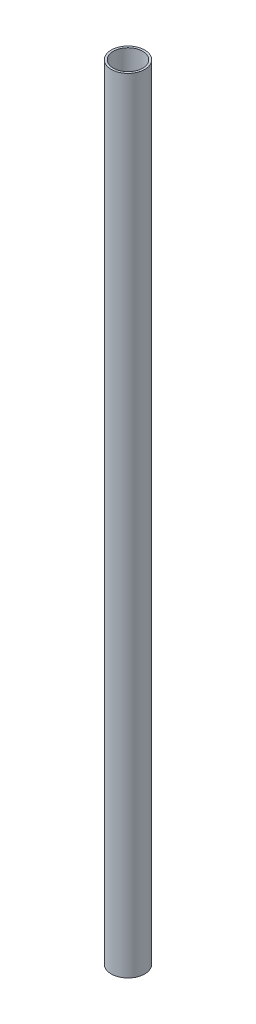
SolidWorks part; units mm, degrees
ref_plane "Спереди" through (0, 0, 0) normal (0, 0, 1) x (1, 0, 0)
ref_plane "Сверху" through (0, 0, 0) normal (0, 1, 0) x (1, 0, 0)
ref_plane "Справа" through (0, 0, 0) normal (1, 0, 0) x (0, 0, -1)
sketch "Эскиз1" plane through (0, 0, 0) normal (0, 1, 0) x (1, 0, 0)
  circle A0 centre (0, 0) radius 6
  circle A1 centre (0, 0) radius 5.25
  dimension "D1" = 10.5
extrude "Бобышка-Вытянуть1" add sketch "Эскиз1" along normal blind 280
